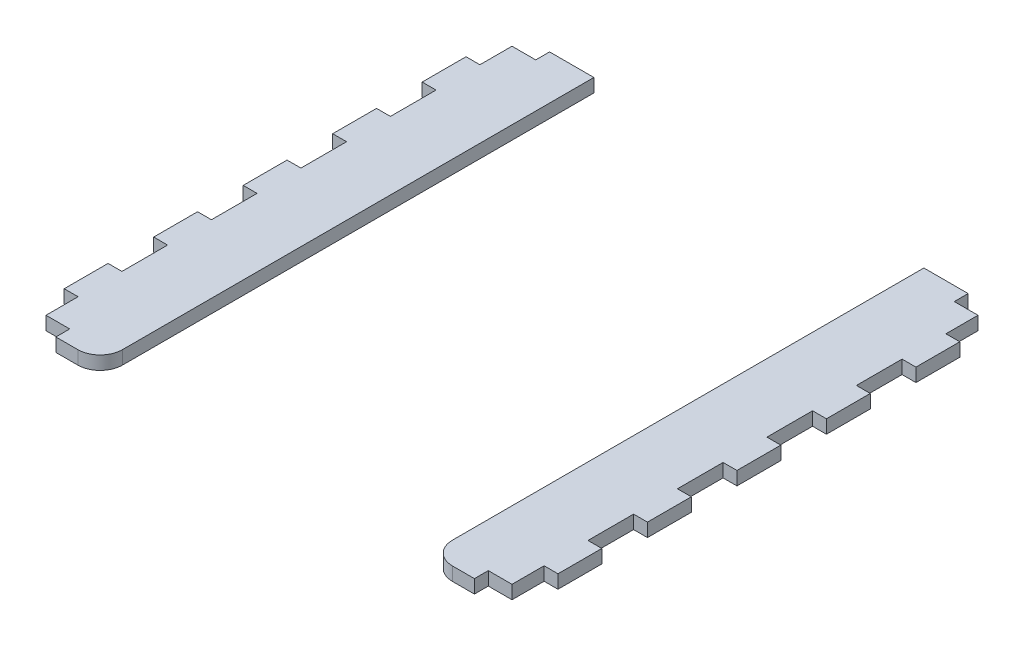
SolidWorks part; units mm, degrees
ref_plane "Front Plane" through (0, 0, 0) normal (0, 0, 1) x (1, 0, 0)
ref_plane "Top Plane" through (0, 0, 0) normal (0, 1, 0) x (1, 0, 0)
ref_plane "Right Plane" through (0, 0, 0) normal (1, 0, 0) x (0, 0, -1)
sketch "Sketch1" plane through (0, 0, 0) normal (0, 1, 0) x (1, 0, 0)
  line L0 (0, 0) -> (0, 21) construction
  line L1 (-55.1722, 66.843) -> (-55.1722, -43.5014) construction
  line L2 (55.1722, -43.5014) -> (-55.1722, -43.5014) construction
  line L3 (55.1722, 66.843) -> (-55.1722, 66.843) construction
  line L4 (55.1722, -43.5014) -> (55.1722, 66.843) construction
  line L5 (-55.1722, 66.843) -> (-55.1722, -43.5014)
  line L6 (55.1722, -43.5014) -> (-55.1722, -43.5014) construction
  line L7 (55.1722, 66.843) -> (-55.1722, 66.843) construction
  line L8 (55.1722, -43.5014) -> (55.1722, 66.843)
  line L9 (36.8722, 66.843) -> (36.8722, -43.5014)
  line L10 (-36.8722, -43.5014) -> (-36.8722, 66.843)
  line L11 (0, 66.843) -> (0, -43.5014) construction
  line L14 (-36.8722, -99.9014) -> (-36.8722, 3.843) construction
  line L15 (55.1722, 66.843) -> (36.8722, 66.843)
  line L16 (-36.8722, 66.843) -> (-55.1722, 66.843)
  line L17 (-55.1722, -43.5014) -> (-36.8722, -43.5014)
  line L18 (36.8722, -43.5014) -> (55.1722, -43.5014)
  circle A0 centre (0, 0) radius 21 construction
  circle A1 centre (0, 0) radius 21 construction
extrude "Boss-Extrude1" add sketch "Sketch1" along normal up to vertex (3 mm away)
fillet "Fillet1" radius 5 1 edges at (-36.8722, 1.5, 43.5014)
fillet "Fillet2" radius 5 1 edges at (36.8722, 1.5, 43.5014)
sketch "Sketch2" plane through (0, 0, 0) normal (0, 1, 0) x (1, 0, 0)
  line L0 (-52.1722, -40.5014) -> (-52.1722, 63.843) construction
  line L1 (-55.1722, 66.843) -> (-55.1722, -43.5014) construction
  line L2 (55.1722, -43.5014) -> (-55.1722, -43.5014) construction
  line L3 (-52.1722, -40.5014) -> (52.1722, -40.5014) construction
  line L4 (55.1722, 66.843) -> (-55.1722, 66.843) construction
  line L5 (52.1722, 63.843) -> (-52.1722, 63.843) construction
  line L6 (-52.1722, -40.5014) -> (-52.1722, 63.843) construction
  line L7 (-55.1722, 66.843) -> (-55.1722, -43.5014) construction
  line L8 (0, -43.5014) -> (-55.1722, -43.5014) construction
  line L9 (-52.1722, -40.5014) -> (0, -40.5014) construction
  line L10 (0, 66.843) -> (-55.1722, 66.843) construction
  line L11 (0, 63.843) -> (-52.1722, 63.843) construction
  line L12 (0, 66.843) -> (0, -43.5014) construction
  line L13 (-52.1722, 16.6708) -> (-55.1722, 16.6708) construction
  line L14 (-46.9722, -40.5014) -> (-46.9722, -43.5014) construction
  line L15 (-46.8722, -40.5014) -> (-46.8722, -43.5014) construction
  line L16 (-46.9722, -42.0014) -> (-46.8722, -42.0014) construction
  line L17 (14.9, 66.843) -> (15, 66.843) construction
  line L19 (46.8722, 66.843) -> (46.8722, 63.843) construction
  line L20 (36.8722, 66.843) -> (36.8722, 63.843) construction
  line L21 (-46.8722, 66.843) -> (-46.8722, 63.843) construction
  line L22 (-36.8722, 66.843) -> (-36.8722, 63.843) construction
  line L23 (-52.1722, 56.6708) -> (-55.1722, 56.6708) construction
  line L24 (-52.1722, 46.6708) -> (-55.1722, 46.6708) construction
  line L25 (-52.1722, 36.6708) -> (-55.1722, 36.6708) construction
  line L26 (-52.1722, 26.6708) -> (-55.1722, 26.6708) construction
  line L27 (0, 11.6708) -> (-55.1722, 11.6708) construction
  line L28 (0, 11.6708) -> (-52.1722, 11.6708) construction
  line L29 (-52.1722, 6.6708) -> (-55.1722, 6.6708) construction
  line L30 (-52.1722, -3.3292) -> (-55.1722, -3.3292) construction
  line L31 (-52.1722, -13.3292) -> (-55.1722, -13.3292) construction
  line L32 (-52.1722, -23.3292) -> (-55.1722, -23.3292) construction
  line L33 (-52.1722, -33.3292) -> (-55.1722, -33.3292) construction
sketch "Sketch3" plane through (0, 0, 0) normal (0, 1, 0) x (1, 0, 0)
  line L0 (-52.0722, -40.4014) -> (-46.7722, -40.4014)
  line L1 (-46.7722, -40.4014) -> (-46.7722, -43.6014)
  line L2 (-46.7722, -43.6014) -> (-55.2722, -43.6014)
  line L3 (-55.2722, -43.6014) -> (-55.2722, -33.2292)
  line L4 (-55.2722, -33.2292) -> (-52.0722, -33.2292)
  line L5 (-52.0722, -33.2292) -> (-52.0722, -40.4014)
  line L6 (-46.7722, 63.743) -> (-46.7722, 66.943)
  line L7 (-46.7722, 66.943) -> (-55.2722, 66.943)
  line L8 (-55.2722, 66.943) -> (-55.2722, 56.5708)
  line L9 (-55.2722, 56.5708) -> (-52.0722, 56.5708)
  line L10 (-52.0722, 56.5708) -> (-52.0722, 63.743)
  line L11 (-52.0722, 63.743) -> (-46.7722, 63.743)
  line L12 (-46.7722, 63.843) -> (-46.8722, 63.843) construction
  line L13 (0, 63.843) -> (-52.1722, 63.843) construction
  line L14 (-52.0722, -13.2292) -> (-55.2722, -13.2292)
  line L16 (-46.8722, 66.843) -> (-46.8722, 63.843) construction
  line L18 (-53.6722, -33.2292) -> (-53.6722, -33.3292) construction
  line L19 (-55.2722, -38.4153) -> (-55.1722, -38.4153) construction
  line L20 (-52.0722, -36.8153) -> (-52.1722, -36.8153) construction
  line L21 (-49.4222, -40.4014) -> (-49.4222, -40.5014) construction
  line L22 (-46.8722, -42.0014) -> (-46.7722, -42.0014) construction
  line L23 (-52.0722, -43.5014) -> (-52.0722, -43.6014) construction
  line L24 (-53.6722, 56.5708) -> (-53.6722, 56.6708) construction
  line L25 (-52.1722, -40.5014) -> (0, -40.5014) construction
  line L26 (-52.1722, -40.5014) -> (-52.1722, 63.843) construction
  line L27 (-52.1722, -33.3292) -> (-55.1722, -33.3292) construction
  line L28 (-55.1722, 66.843) -> (-55.1722, -43.5014) construction
  line L29 (-46.9722, -42.0014) -> (-46.8722, -42.0014) construction
  line L30 (0, -43.5014) -> (-55.1722, -43.5014) construction
  line L31 (-52.1722, 56.6708) -> (-55.1722, 56.6708) construction
  line L32 (0, 11.6708) -> (-55.1722, 11.6708) construction
  line L33 (0, 11.6708) -> (-55.1722, 11.6708) construction
  line L34 (-52.0722, -13.2292) -> (-52.0722, -23.4292)
  line L35 (-52.0722, -23.4292) -> (-55.2722, -23.4292)
  line L36 (-55.2722, -13.2292) -> (-55.2722, -23.4292)
  line L37 (-52.0722, 6.7708) -> (-55.2722, 6.7708)
  line L38 (-52.0722, 6.7708) -> (-52.0722, -3.4292)
  line L39 (-52.0722, -3.4292) -> (-55.2722, -3.4292)
  line L40 (-55.2722, 6.7708) -> (-55.2722, -3.4292)
  line L41 (-53.6722, -23.4292) -> (-53.6722, -23.3292) construction
  line L42 (-53.6722, -13.2292) -> (-53.6722, -13.3292) construction
  line L43 (-53.6722, -3.4292) -> (-53.6722, -3.3292) construction
  line L44 (-53.6722, 6.7708) -> (-53.6722, 6.6708) construction
  line L45 (-52.1722, 6.6708) -> (-55.1722, 6.6708) construction
  line L46 (-52.1722, -3.3292) -> (-55.1722, -3.3292) construction
  line L47 (-52.1722, -13.3292) -> (-55.1722, -13.3292) construction
  line L48 (-52.1722, -23.3292) -> (-55.1722, -23.3292) construction
  line L49 (-52.0722, 16.5708) -> (-55.2722, 16.5708)
  line L50 (-55.2722, 16.5708) -> (-55.2722, 26.7708)
  line L51 (-52.0722, 26.7708) -> (-55.2722, 26.7708)
  line L52 (-52.0722, 16.5708) -> (-52.0722, 26.7708)
  line L53 (-52.0722, 36.5708) -> (-55.2722, 36.5708)
  line L54 (-55.2722, 36.5708) -> (-55.2722, 46.7708)
  line L55 (-52.0722, 46.7708) -> (-55.2722, 46.7708)
  line L56 (-52.0722, 36.5708) -> (-52.0722, 46.7708)
  line L57 (0, -43.5014) -> (0, 66.843) construction
extrude "Cut-Extrude1" cut sketch "Sketch3" along normal through all
sketch "Sketch4" plane through (0, 0, 0) normal (0, 1, 0) x (1, 0, 0)
  line L0 (0, 66.843) -> (0, -43.5014) construction
  line L1 (0, 66.843) -> (0, -43.5014) construction
  line L2 (52.0722, 36.5708) -> (52.0722, 46.7708)
  line L3 (55.2722, 36.5708) -> (52.0722, 36.5708)
  line L4 (-52.0722, 6.7708) -> (-55.2722, 6.7708)
  line L5 (-55.2722, 6.7708) -> (-55.2722, -3.4292)
  line L6 (-46.7722, 63.743) -> (-46.7722, 66.943)
  line L7 (-46.7722, 66.943) -> (-55.2722, 66.943)
  line L8 (-55.2722, 66.943) -> (-55.2722, 56.5708)
  line L9 (-55.2722, 56.5708) -> (-52.0722, 56.5708)
  line L10 (-52.0722, 56.5708) -> (-52.0722, 63.743)
  line L11 (-52.0722, 63.743) -> (-46.7722, 63.743)
  line L12 (-46.7722, 63.743) -> (-46.7722, 66.943) construction
  line L13 (-46.7722, 66.943) -> (-55.2722, 66.943) construction
  line L14 (-55.2722, 66.943) -> (-55.2722, 56.5708) construction
  line L15 (-55.2722, 56.5708) -> (-52.0722, 56.5708) construction
  line L16 (-52.0722, 56.5708) -> (-52.0722, 63.743) construction
  line L17 (-52.0722, 63.743) -> (-46.7722, 63.743) construction
  line L18 (-46.7722, -40.4014) -> (-52.0722, -40.4014)
  line L19 (-46.7722, -43.6014) -> (-46.7722, -40.4014)
  line L20 (-55.2722, -43.6014) -> (-46.7722, -43.6014)
  line L21 (-55.2722, -33.2292) -> (-55.2722, -43.6014)
  line L22 (-52.0722, -33.2292) -> (-55.2722, -33.2292)
  line L23 (-52.0722, -40.4014) -> (-52.0722, -33.2292)
  line L24 (-46.7722, -40.4014) -> (-52.0722, -40.4014) construction
  line L25 (-46.7722, -43.6014) -> (-46.7722, -40.4014) construction
  line L26 (-55.2722, -43.6014) -> (-46.7722, -43.6014) construction
  line L27 (-55.2722, -33.2292) -> (-55.2722, -43.6014) construction
  line L28 (-52.0722, -33.2292) -> (-55.2722, -33.2292) construction
  line L29 (-52.0722, -40.4014) -> (-52.0722, -33.2292) construction
  line L30 (-55.2722, -3.4292) -> (-52.0722, -3.4292)
  line L31 (-52.0722, -3.4292) -> (-52.0722, 6.7708)
  line L32 (-52.0722, 6.7708) -> (-55.2722, 6.7708) construction
  line L33 (-55.2722, 6.7708) -> (-55.2722, -3.4292) construction
  line L34 (-55.2722, -3.4292) -> (-52.0722, -3.4292) construction
  line L35 (-52.0722, -3.4292) -> (-52.0722, 6.7708) construction
  line L36 (-52.0722, -13.2292) -> (-55.2722, -13.2292)
  line L37 (-52.0722, -23.4292) -> (-52.0722, -13.2292)
  line L38 (-55.2722, -23.4292) -> (-52.0722, -23.4292)
  line L39 (-55.2722, -13.2292) -> (-55.2722, -23.4292)
  line L40 (-52.0722, -13.2292) -> (-55.2722, -13.2292) construction
  line L41 (-52.0722, -23.4292) -> (-52.0722, -13.2292) construction
  line L42 (-55.2722, -23.4292) -> (-52.0722, -23.4292) construction
  line L43 (-55.2722, -13.2292) -> (-55.2722, -23.4292) construction
  line L44 (-55.2722, 16.5708) -> (-52.0722, 16.5708)
  line L45 (-55.2722, 26.7708) -> (-55.2722, 16.5708)
  line L46 (-52.0722, 26.7708) -> (-55.2722, 26.7708)
  line L47 (-52.0722, 16.5708) -> (-52.0722, 26.7708)
  line L48 (-55.2722, 16.5708) -> (-52.0722, 16.5708) construction
  line L49 (-55.2722, 26.7708) -> (-55.2722, 16.5708) construction
  line L50 (-52.0722, 26.7708) -> (-55.2722, 26.7708) construction
  line L51 (-52.0722, 16.5708) -> (-52.0722, 26.7708) construction
  line L52 (-52.0722, 46.7708) -> (-55.2722, 46.7708)
  line L53 (-55.2722, 46.7708) -> (-55.2722, 36.5708)
  line L54 (-55.2722, 36.5708) -> (-52.0722, 36.5708)
  line L55 (-52.0722, 36.5708) -> (-52.0722, 46.7708)
  line L56 (-52.0722, 46.7708) -> (-55.2722, 46.7708) construction
  line L57 (-55.2722, 46.7708) -> (-55.2722, 36.5708) construction
  line L58 (-55.2722, 36.5708) -> (-52.0722, 36.5708) construction
  line L59 (-52.0722, 36.5708) -> (-52.0722, 46.7708) construction
  line L60 (55.2722, 46.7708) -> (55.2722, 36.5708)
  line L61 (52.0722, 46.7708) -> (55.2722, 46.7708)
  line L62 (52.0722, 16.5708) -> (52.0722, 26.7708)
  line L63 (52.0722, 26.7708) -> (55.2722, 26.7708)
  line L64 (55.2722, 26.7708) -> (55.2722, 16.5708)
  line L65 (55.2722, 16.5708) -> (52.0722, 16.5708)
  line L66 (55.2722, -13.2292) -> (55.2722, -23.4292)
  line L67 (55.2722, -23.4292) -> (52.0722, -23.4292)
  line L68 (52.0722, -23.4292) -> (52.0722, -13.2292)
  line L69 (52.0722, -13.2292) -> (55.2722, -13.2292)
  line L70 (52.0722, -3.4292) -> (52.0722, 6.7708)
  line L71 (55.2722, -3.4292) -> (52.0722, -3.4292)
  line L72 (55.2722, 6.7708) -> (55.2722, -3.4292)
  line L73 (52.0722, 6.7708) -> (55.2722, 6.7708)
  line L74 (52.0722, -40.4014) -> (52.0722, -33.2292)
  line L75 (52.0722, -33.2292) -> (55.2722, -33.2292)
  line L76 (55.2722, -33.2292) -> (55.2722, -43.6014)
  line L77 (55.2722, -43.6014) -> (46.7722, -43.6014)
  line L78 (46.7722, -43.6014) -> (46.7722, -40.4014)
  line L79 (46.7722, -40.4014) -> (52.0722, -40.4014)
  line L80 (52.0722, 63.743) -> (46.7722, 63.743)
  line L81 (52.0722, 56.5708) -> (52.0722, 63.743)
  line L82 (55.2722, 56.5708) -> (52.0722, 56.5708)
  line L83 (55.2722, 66.943) -> (55.2722, 56.5708)
  line L84 (46.7722, 66.943) -> (55.2722, 66.943)
  line L85 (46.7722, 63.743) -> (46.7722, 66.943)
  dimension "D1" = 0
  dimension "D2" = 0
  dimension "D3" = 0
  dimension "D4" = 0
  dimension "D5" = 0
  dimension "D6" = 0
extrude "Cut-Extrude2" cut sketch "Sketch4" along normal through all
